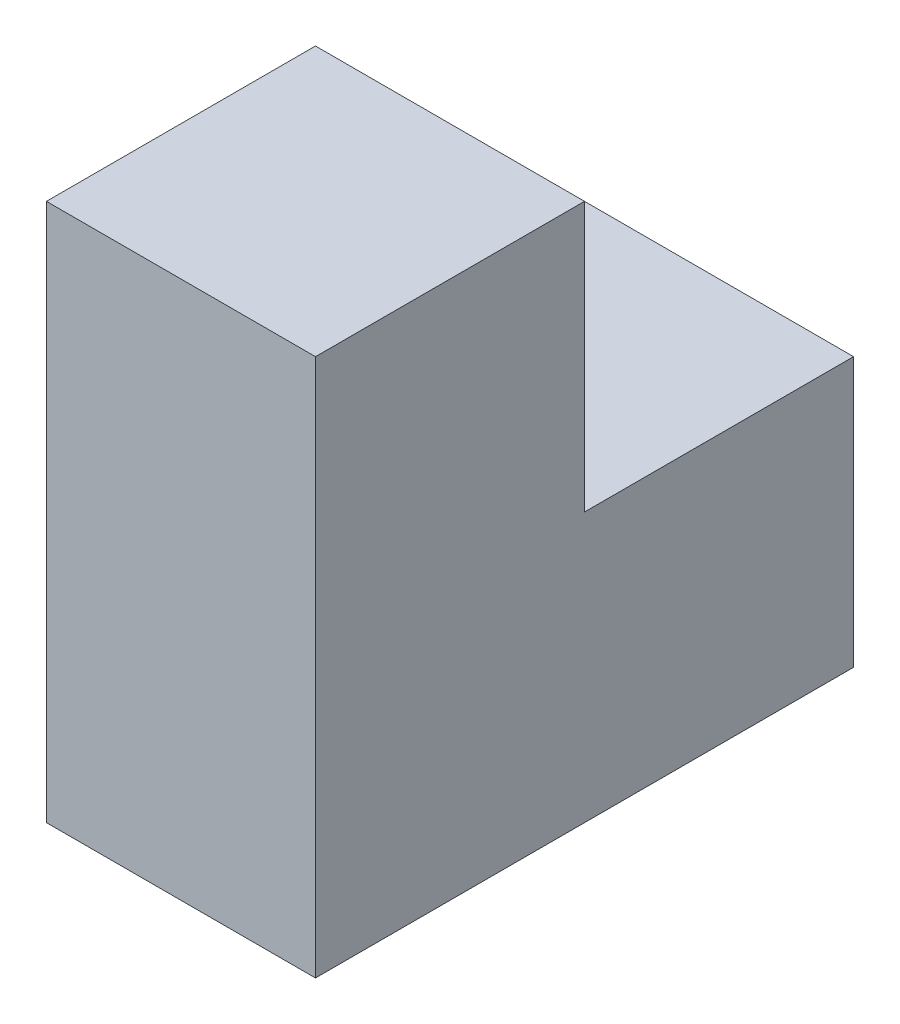
SolidWorks part; units mm, degrees
ref_plane "Plan de face" through (0, 0, 0) normal (0, 0, 1) x (1, 0, 0)
ref_plane "Plan de dessus" through (0, 0, 0) normal (0, 1, 0) x (1, 0, 0)
ref_plane "Plan de droite" through (0, 0, 0) normal (1, 0, 0) x (0, 0, -1)
sketch "Esquisse1" plane through (0, 0, 0) normal (1, 0, 0) x (0, 0, -1)
  line L0 (0, 0) -> (60, 0)
  line L1 (60, 0) -> (60, 30)
  line L2 (60, 30) -> (30, 30)
  line L3 (30, 30) -> (30, 60)
  line L4 (30, 60) -> (0, 60)
  line L5 (0, 60) -> (0, 0)
  dimension "D1" = 30
  dimension "D2" = 60
  dimension "D3" = 60
  dimension "D4" = 30
extrude "Boss.-Extru.1" add sketch "Esquisse1" along normal blind 30
